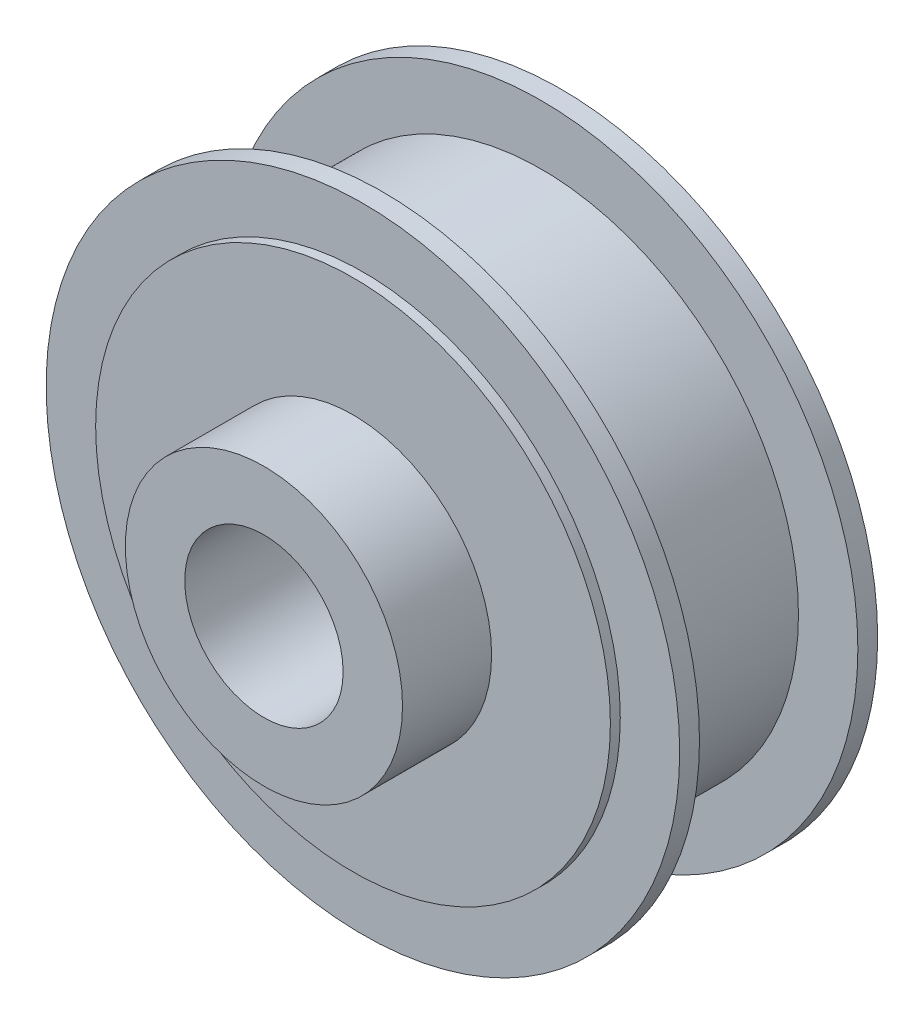
SolidWorks part; units mm, degrees
ref_plane "Plan de face" through (0, 0, 0) normal (0, 0, 1) x (1, 0, 0)
ref_plane "Plan de dessus" through (0, 0, 0) normal (0, 1, 0) x (1, 0, 0)
ref_plane "Plan de droite" through (0, 0, 0) normal (1, 0, 0) x (0, 0, -1)
sketch "Esquisse1" plane through (0, 0, 0) normal (0, 0, 1) x (1, 0, 0)
  circle A0 centre (0, 0) radius 16
  dimension "D1" = 32
extrude "Boss.-Extru.1" add sketch "Esquisse1" along normal blind 1 contours A0
sketch "Esquisse2" plane through (0, 0, 1) normal (0, 0, 1) x (1, 0, 0)
  circle A0 centre (0, 0) radius 13
extrude "Boss.-Extru.2" add sketch "Esquisse2" along normal blind 8
sketch "Esquisse3" plane through (0, 0, 9) normal (0, 0, 1) x (1, 0, 0)
  circle A0 centre (0, 0) radius 16
extrude "Boss.-Extru.3" add sketch "Esquisse3" along normal blind 1
sketch "Esquisse4" plane through (0, 0, 10) normal (0, 0, 1) x (1, 0, 0)
  circle A0 centre (0, 0) radius 7
extrude "Boss.-Extru.4" add sketch "Esquisse4" along normal blind 5
sketch "Esquisse6" plane through (0, 0, 10) normal (0, 0, 1) x (1, 0, 0)
  circle A0 centre (0, 0) radius 13
extrude "Boss.-Extru.5" add sketch "Esquisse6" along normal blind 0.5 contours A0
sketch "Esquisse7" plane through (0, 0, 0) normal (0, 0, -1) x (-1, 0, 0)
  circle A0 centre (0, 0) radius 13
extrude "Boss.-Extru.6" add sketch "Esquisse7" along normal blind 0.5
sketch "Esquisse8" plane through (0, 0, 15) normal (0, 0, 1) x (1, 0, 0)
  circle A0 centre (0, 0) radius 4
extrude "Enlèv. mat.-Extru.2" cut sketch "Esquisse8" against normal blind 16 contours A0
